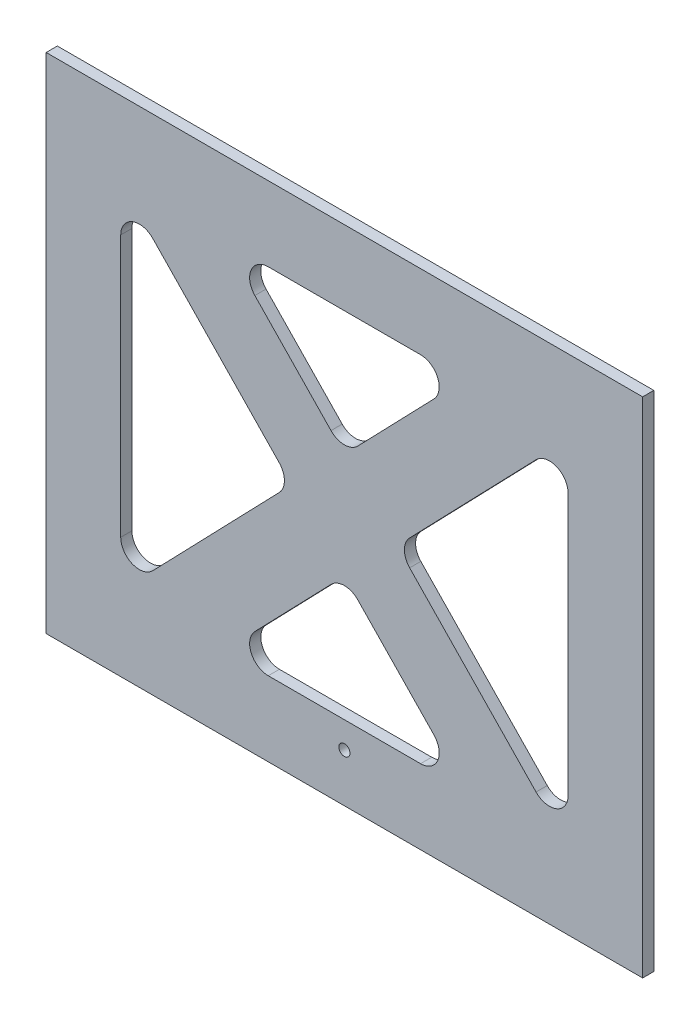
SolidWorks part; units mm, degrees
material "birch 3mm plywood"
ref_plane "Front Plane" through (0, 0, 0) normal (0, 0, 1) x (1, 0, 0)
ref_plane "Top Plane" through (0, 0, 0) normal (0, 1, 0) x (1, 0, 0)
ref_plane "Right Plane" through (0, 0, 0) normal (1, 0, 0) x (0, 0, -1)
sketch "Sketch1" plane through (0, 0, 152) normal (0, 0, 1) x (1, 0, 0)
  line L1 (-80, 80.4171) -> (80, 80.4171)
  line L2 (-80, 80.4171) -> (-80, -54.5829)
  line L3 (-80, -54.5829) -> (80, -54.5829)
  line L4 (80, 80.4171) -> (80, -54.5829)
  line L6 (-60, -22.2046) -> (-60, 48.0389)
  line L7 (-51.4028, 51.5116) -> (-17.4968, 16.3899)
  line L12 (78, -49.5829) -> (-78, -49.5829) construction
  line L13 (78, 75.4171) -> (78, -49.5829) construction
  line L14 (-78, -49.5829) -> (-78, 75.4171) construction
  line L15 (-78, 75.4171) -> (78, 75.4171) construction
  line L18 (20.4243, 60.4171) -> (-20.4243, 60.4171)
  line L19 (-17.4968, 9.4444) -> (-51.4028, -25.6773)
  line L20 (-24.0216, 51.9444) -> (-3.5972, 30.7877)
  line L21 (3.5972, 30.7877) -> (24.0216, 51.9444)
  line L22 (80, 80.4171) -> (80, 77.4171) construction
  line L23 (51.4028, 51.5116) -> (17.4968, 16.3899)
  line L24 (60, -22.2046) -> (60, 48.0389)
  line L25 (17.4968, 9.4444) -> (51.4028, -25.6773)
  line L26 (-78, 12.9171) -> (78, 12.9171) construction
  line L27 (-24.0216, -26.1101) -> (-3.5972, -4.9534)
  line L28 (20.4243, -34.5829) -> (-20.4243, -34.5829)
  line L29 (3.5972, -4.9534) -> (24.0216, -26.1101)
  line L30 (0, 27.0615) -> (0, -1.2272) construction
  line L31 (-14.1443, 12.9171) -> (14.1443, 12.9171) construction
  line L32 (0, 27.0615) -> (0, -1.2272) construction
  line L34 (-80, -54.5829) -> (-80, 77.4171) construction
  line L36 (80, 80.4171) -> (-80, 80.4171) construction
  line L37 (75, -49.5829) -> (-75, -49.5829) construction
  arc A0 (-51.4028, -25.6773) -> (-60, -22.2046) centre (-55, -22.2046) cw
  arc A1 (-17.4968, 9.4444) -> (-17.4968, 16.3899) centre (-21.0941, 12.9171) ccw
  arc A2 (-51.4028, 51.5116) -> (-60, 48.0389) centre (-55, 48.0389) ccw
  arc A3 (24.0216, -26.1101) -> (20.4243, -34.5829) centre (20.4243, -29.5829) cw
  arc A4 (-24.0216, -26.1101) -> (-20.4243, -34.5829) centre (-20.4243, -29.5829) ccw
  arc A5 (-3.5972, -4.9534) -> (3.5972, -4.9534) centre (0, -8.4261) cw
  arc A6 (17.4968, 16.3899) -> (17.4968, 9.4444) centre (21.0941, 12.9171) ccw
  arc A7 (51.4028, -25.6773) -> (60, -22.2046) centre (55, -22.2046) ccw
  arc A8 (60, 48.0389) -> (51.4028, 51.5116) centre (55, 48.0389) ccw
  arc A9 (-24.0216, 51.9444) -> (-20.4243, 60.4171) centre (-20.4243, 55.4171) cw
  arc A10 (24.0216, 51.9444) -> (20.4243, 60.4171) centre (20.4243, 55.4171) ccw
  arc A11 (3.5972, 30.7877) -> (-3.5972, 30.7877) centre (0, 34.2604) cw
  point P14 (0, 12.9171)
  point P15 (0, 12.9171)
  point P32 (-60, 60.4171)
  point P35 (32.201, -34.5829)
  point P38 (-32.201, -34.5829)
  point P51 (-32.201, 60.4171)
  point P54 (32.201, 60.4171)
  dimension "D9" = 5
  dimension "D10" = 5
  dimension "D1" = 2
  dimension "D2" = 2
  dimension "D3" = 5
  dimension "D4" = 5
  dimension "D5" = 20
  dimension "D6" = 20
  dimension "D7" = 20
  dimension "D8" = 20
extrude "Boss-Extrude1" add sketch "Sketch1" along normal blind 3
sketch "Sketch2" plane through (0, 0, 155) normal (0, 0, 1) x (1, 0, 0)
  line L0 (-80, -41.6319) -> (80, -41.6319)
  line L1 (-80, 80.4171) -> (-80, -54.5829) construction
  line L2 (80, -54.5829) -> (80, 80.4171) construction
  circle A0 centre (0, -41.6319) radius 1.5
extrude "Cut-Extrude1" cut sketch "Sketch2" against normal blind 20 contours L0 A0 | L0 A0
